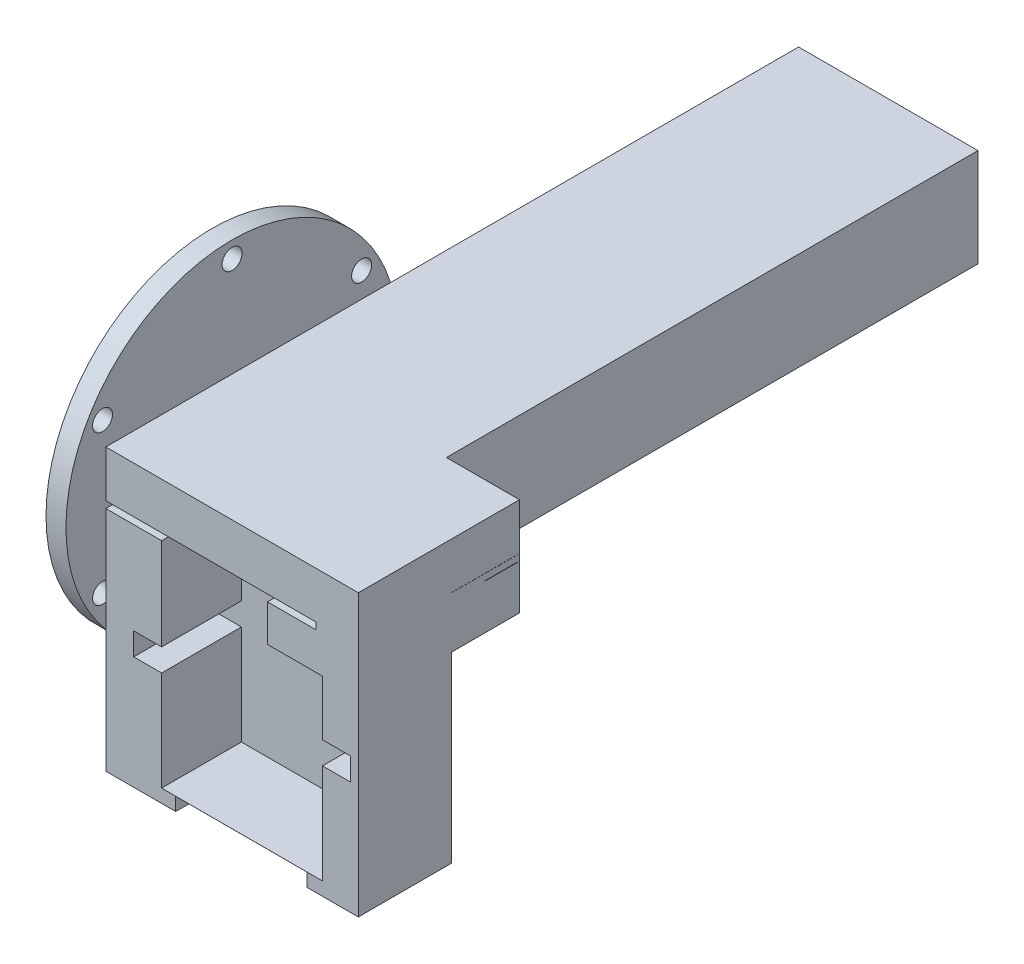
SolidWorks part; units mm, degrees
ref_plane "前视基准面" through (0, 0, 0) normal (0, 0, 1) x (1, 0, 0)
ref_plane "上视基准面" through (0, 0, 0) normal (0, 1, 0) x (1, 0, 0)
ref_plane "右视基准面" through (0, 0, 0) normal (1, 0, 0) x (0, 0, -1)
sketch "草图2" plane through (0, 0, 6) normal (0, 0, 1) x (1, 0, 0)
  line L0 (29.8673, 15.5624) -> (29.0149, 15.5624)
  line L1 (29.0149, 15.5624) -> (29.0149, 12.2624)
  line L2 (29.0149, 12.2624) -> (24.8149, 12.2624)
  line L3 (24.8149, 12.2624) -> (24.8149, 8.8624)
  line L4 (24.8149, 8.8624) -> (29.0149, 8.8624)
  line L5 (29.0149, 8.8624) -> (29.0149, -6.1376)
  line L6 (29.0149, -6.1376) -> (53.2196, -6.1376)
  line L8 (58.6173, -8.1376) -> (23.6173, -8.1376)
  line L9 (23.6173, -8.1376) -> (23.6173, 15.5624)
  line L10 (23.6173, 15.5624) -> (29.0149, 15.5624)
  line L11 (58.6173, 15.5624) -> (53.2196, 15.5624)
  line L12 (58.6173, -8.1376) -> (58.6173, 15.5624)
  line L13 (53.2196, 8.8624) -> (53.2196, -6.1376)
  line L14 (57.4196, 8.8624) -> (53.2196, 8.8624)
  line L15 (57.4196, 12.2624) -> (57.4196, 8.8624)
  line L16 (53.2196, 12.2624) -> (57.4196, 12.2624)
  line L17 (53.2196, 15.5624) -> (53.2196, 12.2624)
extrude "凸台-拉伸1" add sketch "草图2" against normal blind 14 contours L11 L17 L16 L15 L14 L13 L6 L5 L4 L3 L2 L1 L10 L9 L8 L12
sketch "草图3" plane through (0, 0, -8) normal (0, 0, -1) x (-1, 0, 0)
  line L0 (-58.6173, -8.1376) -> (-23.6173, -8.1376) construction
  line L1 (-58.6173, 15.5624) -> (-23.6281, 15.5624)
  line L2 (-58.6173, 15.5624) -> (-58.6173, -8.1376)
  line L3 (-58.6173, -8.1376) -> (-23.6281, -8.1376)
  line L4 (-23.6281, 15.5624) -> (-23.6281, -8.1376)
extrude "凸台-拉伸2" add sketch "草图3" against normal blind 1.99
sketch "草图4" plane through (0, -8.1376, 0) normal (0, -1, 0) x (1, 0, 0)
  line L0 (58.6173, 6) -> (23.6173, 6) construction
  line L1 (31.1325, 6) -> (50.872, 6)
  line L2 (31.1325, 6) -> (31.1325, -8)
  line L3 (31.1325, -8) -> (50.872, -8)
  line L4 (50.872, 6) -> (50.872, -8)
  line L5 (58.6173, -8) -> (23.6173, -8) construction
extrude "切除-拉伸1" cut sketch "草图4" against normal blind 1.99
sketch "草图5" plane through (0, 27.1124, 0) normal (0, 1, 0) x (1, 0, 0)
  circle A0 centre (35.6173, 0) radius 17.25
sketch "草图6" plane through (0, 26.1124, 0) normal (0, -1, 0) x (1, 0, 0)
  line L0 (35.6173, -17.25) -> (35.6173, -8.75)
  line L1 (35.6173, 17.25) -> (35.6173, 8.75)
  line L2 (35.6173, 8.75) -> (20.7512, 8.75)
  line L3 (35.6173, 8.75) -> (50.4833, 8.75)
  circle A0 centre (35.6173, 0) radius 17.25
sketch "草图7" plane through (0, 15.5624, 0) normal (0, 1, 0) x (1, 0, 0)
  line L0 (23.6173, -6) -> (23.6173, 8)
  line L1 (23.6173, 8) -> (23.6173, -6) construction
  line L2 (58.6173, 8) -> (23.6173, 8) construction
  line L3 (23.6173, 8) -> (58.6173, 8)
  line L4 (58.6173, 8) -> (58.6173, -6)
  line L5 (58.6173, -6) -> (53.2196, -6) construction
  line L6 (58.6173, 8) -> (58.6173, -6) construction
  line L7 (58.6173, -6) -> (53.2196, -6)
  line L8 (53.2196, -6) -> (53.2196, 6.01)
  line L9 (53.2196, 6.01) -> (29.0149, 6.01)
  line L10 (29.0149, 6.01) -> (29.0149, -6)
  line L11 (29.0149, -6) -> (23.6173, -6)
extrude "凸台-拉伸3" add sketch "草图7" along normal blind 4.99 contours L11 L0 L3 L4 L7 L8 L9 L10
sketch "草图8" plane through (0, 20.5524, 0) normal (0, 1, 0) x (1, 0, 0)
  line L0 (23.6173, -6) -> (29.0149, -6)
  line L1 (23.6173, 8) -> (23.6173, -6) construction
  line L2 (23.6173, -6) -> (29.0149, -6) construction
  line L3 (29.0149, -6) -> (29.0149, 6.01)
  line L4 (29.0149, 6.01) -> (44.9535, 6.01)
  line L5 (29.0149, 6.01) -> (53.2196, 6.01) construction
  line L6 (44.9535, 6.01) -> (44.9535, -6)
  line L7 (44.9535, -6) -> (58.6173, -6)
  line L8 (58.6173, -6) -> (58.6173, 8) construction
  line L9 (58.6173, -6) -> (58.6173, 8)
  line L10 (58.6173, 8) -> (23.6173, 8)
  line L11 (58.6173, 8) -> (23.6173, 8) construction
  line L12 (23.6173, 8) -> (23.6173, -6)
extrude "凸台-拉伸4" add sketch "草图8" along normal blind 5.55 contours L12 L0 L3 L4 L6 L7 L9 L10
sketch "草图11" plane through (0, 26.1024, 0) normal (0, 1, 0) x (1, 0, 0)
  line L0 (51.3501, 8) -> (58.6173, 8)
  line L1 (58.6173, 8) -> (23.6173, 8) construction
  line L2 (58.6173, 8) -> (58.6173, -6)
  line L3 (44.9535, -6) -> (58.6173, -6) construction
  line L4 (58.6173, -6) -> (58.6173, 8) construction
  line L5 (58.6173, -6) -> (52.2161, -6)
  arc A0 (52.2161, -6) -> (51.3501, 8) centre (35.6173, 0) ccw
extrude "凸台-拉伸5" add sketch "草图11" along normal blind 1.02
sketch "草图13" plane through (0, 27.1224, 0) normal (0, 1, 0) x (1, 0, 0)
  line L0 (23.6173, -6) -> (29.0149, -6) construction
  line L1 (58.6173, 8) -> (23.6173, 8)
  line L2 (58.6173, 8) -> (58.6173, -6)
  line L3 (58.6173, -6) -> (23.6173, -6)
  line L4 (23.6173, 8) -> (23.6173, -6)
  line L5 (23.6173, 8) -> (23.6173, -6) construction
extrude "凸台-拉伸6" add sketch "草图13" along normal blind 4
sketch "草图14" plane through (23.6173, 0, 0) normal (-1, 0, 0) x (0, 0, 1)
  line L0 (-8, 27.1224) -> (-8, 26.1024)
  line L1 (-8, 26.6124) -> (-13, 26.6124)
  line L2 (-8, 26.1024) -> (-8.7807, 26.1024)
  line L3 (-8, 27.1224) -> (-8.7807, 27.1224)
  line L4 (-13, 30.8624) -> (-8, 30.8624)
  line L5 (-8, 31.1224) -> (-8, 27.1224) construction
  line L6 (-13, 22.3624) -> (-8, 22.3624)
  line L7 (-8, -8.1376) -> (-8, 26.1024) construction
  line L8 (-8, 30.8624) -> (-8, 22.3624)
  line L9 (-8, 30.8624) -> (-8, 31.1224)
  line L10 (-8, 31.1224) -> (-13, 31.1224)
  line L11 (-13, 31.1224) -> (-13, 30.8624)
  line L12 (-13, 22.3624) -> (-13, 20.3624)
  line L13 (-13, 20.3624) -> (-8, 20.3624)
  line L14 (-8, 20.3624) -> (-8, 22.3624)
  circle A1 centre (-13, 26.6124) radius 4.25
  line M3 (-8, 26.1024) -> (-8, -8.1376)
extrude "凸台-拉伸8" add sketch "草图14" against normal blind 21 contours L12 L13 L6 M3 | A1 L6 L2 M3 | A1 L3 L8 L4
sketch "草图15" plane through (44.6173, 0, 0) normal (1, 0, 0) x (0, 0, -1)
  line L2 (13, 20.3624) -> (8, 20.3624)
  line L3 (13, 20.3624) -> (13, 26.1024)
  line L4 (13, 26.1024) -> (8, 26.1024)
  line L5 (8, 20.3624) -> (8, 26.1024)
  line L6 (13, 31.1224) -> (8, 31.1224)
  line L7 (13, 31.1224) -> (13, 27.1224)
  line L8 (13, 27.1224) -> (8, 27.1224)
  line L9 (8, 31.1224) -> (8, 27.1224)
extrude "凸台-拉伸9" add sketch "草图15" along normal blind 14
sketch "草图16" plane through (0, 26.1024, 0) normal (0, 1, 0) x (1, 0, 0)
  line L0 (47.4815, 13) -> (58.6173, 13)
  line L1 (58.6173, 13) -> (44.6173, 13) construction
  line L2 (58.6173, 13) -> (58.6173, 8)
  line L3 (58.6173, 13) -> (58.6173, 8) construction
  line L4 (58.6173, 8) -> (51.294, 8)
  arc A0 (51.294, 8) -> (47.4815, 13) centre (35.6173, 0) ccw
extrude "凸台-拉伸10" add sketch "草图16" along normal blind 1
sketch "草图17" plane through (0, 31.1224, 0) normal (0, 1, 0) x (1, 0, 0)
  line L0 (23.6173, -6) -> (58.6173, -6) construction
  line L1 (23.6173, 13) -> (58.6173, 13)
  line L2 (23.6173, 13) -> (23.6173, -6)
  line L3 (23.6173, -6) -> (58.6173, -6)
  line L4 (58.6173, 13) -> (58.6173, -6)
extrude "凸台-拉伸11" add sketch "草图17" along normal blind 3
sketch "草图18" plane through (0, 20.3624, 0) normal (0, -1, 0) x (1, 0, 0)
  line L1 (23.6173, -8) -> (58.6173, -8)
  line L2 (23.6173, -8) -> (23.6173, -13)
  line L3 (23.6173, -13) -> (58.6173, -13)
  line L4 (58.6173, -8) -> (58.6173, -13)
extrude "凸台-拉伸12" add sketch "草图18" along normal blind 1
sketch "草图19" plane through (23.6173, 0, 0) normal (-1, 0, 0) x (0, 0, 1)
  line L0 (-8, 19.3624) -> (-17.25, 19.3624)
  line L1 (6, -8.1376) -> (-8, -8.1376)
  line L2 (6, -8.1376) -> (6, 19.3624)
  line L3 (6, 19.3624) -> (-8, 19.3624)
  line L4 (-8, -8.1376) -> (-8, 19.3624)
  line L13 (-17.25, 19.3624) -> (-17.25, 34.1224)
  line L14 (-17.25, 34.1224) -> (6, 34.1224)
  line L15 (6, 34.1224) -> (6, 27.1224)
  line L16 (6, 34.1224) -> (6, 27.1224) construction
  line L17 (6, 27.1224) -> (-8.7807, 27.1224)
  line L18 (-8.7807, 26.1024) -> (6, 26.1024)
  line L19 (6, 26.1024) -> (6, 19.3624)
  line L20 (-17.25, 19.3624) -> (6, 19.3624)
  line L21 (-13, 22.3624) -> (-17.25, 22.3624)
  line L22 (-13, 30.8624) -> (-17.25, 30.8624)
  line L23 (-17.25, 19.3624) -> (-18.25, 19.3624)
  line L24 (-18.25, 19.3624) -> (-18.25, 34.1224)
  line L25 (-18.25, 34.1224) -> (-17.25, 34.1224)
  line L26 (-18.25, 34.1224) -> (-17.25, 34.1224)
  line L27 (-18.25, 19.3624) -> (-17.25, 19.3624)
  circle A0 centre (-13, 26.6124) radius 4.25
  line M14 (6, -8.1376) -> (6, 26.1024)
  line M15 (6, 26.1024) -> (-8.7807, 26.1024)
  arc M16 (-8.7807, 26.1024) -> (-13, 22.3624) centre (-13, 26.6124) cw
  line M17 (-13, 22.3624) -> (-13, 19.3624)
  line M18 (-13, 19.3624) -> (-8, 19.3624)
  line M19 (-8, 19.3624) -> (-8, -8.1376)
  line M20 (-8, -8.1376) -> (6, -8.1376)
extrude "凸台-拉伸16" add sketch "草图19" along normal blind 3 contours L3 M14 M15 M16 M17 M18 | A0 L17 L15 L14 L13 L22 | L21 L13 L0 M17 | L3 M14 M19 M20 | L25 L24 L23 L13 | A0 L13 L21 | A0 L22 L13
sketch "草图20" plane through (23.6173, 0, 0) normal (1, 0, 0) x (0, 0, -1)
  line L0 (13, 19.3624) -> (18.25, 19.3624)
  line L1 (18.25, 19.3624) -> (18.25, 22.3624)
  line L2 (18.25, 19.3624) -> (18.25, 34.1224) construction
  line L3 (18.25, 22.3624) -> (13, 22.3624)
  line L4 (13, 30.8624) -> (18.25, 30.8624)
  line L5 (13, 34.1224) -> (13, 30.8624) construction
  line L6 (18.25, 30.8624) -> (18.25, 34.1224)
  line L7 (18.25, 34.1224) -> (13, 34.1224) construction
  line L8 (18.25, 34.1224) -> (13, 34.1224)
  line L9 (13, 34.1224) -> (13, 30.8624)
  arc A0 (13, 22.3624) -> (13, 30.8624) centre (13, 26.6124) ccw construction
  line M1 (13, 22.3624) -> (13, 19.3624)
  line M2 (13, 19.3624) -> (18.25, 19.3624)
  line M3 (18.25, 19.3624) -> (18.25, 34.1224)
  line M4 (18.25, 34.1224) -> (13, 34.1224)
  line M5 (13, 34.1224) -> (13, 30.8624)
extrude "凸台-拉伸18" add sketch "草图20" along normal blind 35 contours L4 M5 M3 M4 | L3 M3 M1 M2
sketch "草图21" plane through (0, 0, -13) normal (0, 0, -1) x (-1, 0, 0)
  line L0 (-58.6173, 22.3624) -> (-58.6173, 27.1024) construction
  line L1 (-58.6173, 30.8624) -> (-44.6173, 30.8624)
  line L2 (-58.6173, 30.8624) -> (-58.6173, 27.1224)
  line L3 (-58.6173, 27.1224) -> (-44.6173, 27.1224)
  line L4 (-44.6173, 30.8624) -> (-44.6173, 27.1224)
  line L5 (-44.6173, 22.3624) -> (-58.6173, 22.3624)
  line L6 (-44.6173, 22.3624) -> (-44.6173, 26.1124)
  line L7 (-44.6173, 26.1124) -> (-58.6173, 26.1124)
  line L8 (-58.6173, 22.3624) -> (-58.6173, 26.1124)
extrude "凸台-拉伸19" add sketch "草图21" along normal blind 5
sketch "草图22" plane through (58.6173, 0, 0) normal (1, 0, 0) x (0, 0, -1)
  line L0 (18.25, 22.3624) -> (18.25, 30.8624) construction
  line L1 (13, 27.1024) -> (18.25, 27.1024)
  line L2 (13, 27.1024) -> (13, 26.1558)
  line L3 (13, 26.1558) -> (18.25, 26.1558)
  line L4 (18.25, 27.1024) -> (18.25, 26.1558)
  line L6 (18, 30.8624) -> (18.25, 30.8624)
  line L7 (18, 30.8624) -> (18, 22.3624)
  line L8 (18, 22.3624) -> (18.25, 22.3624)
  line L9 (18.25, 30.8624) -> (18.25, 22.3624)
  line M2 (13, 26.1124) -> (13, 27.1024)
extrude "凸台-拉伸20" add sketch "草图22" against normal blind 11 contours L7 L1 L3 M2
ref_plane "基准面5" through (47.6173, 30.8624, -18.25) normal (0, -1, 0) x (-1, 0, 0)
sketch "草图26" plane through (47.6173, 0, 0) normal (-1, 0, 0) x (0, 0, 1)
  line L0 (-20.5875, 30.8624) -> (-15.9125, 30.8624) construction
  line L1 (-18.25, 30.8624) -> (-18, 30.8624)
  line L2 (-18.25, 30.8624) -> (-18.25, 22.3624)
  line L3 (-18.25, 22.3624) -> (-18, 22.3624)
  line L4 (-18, 30.8624) -> (-18, 22.3624)
  line L5 (-18.25, 19.3624) -> (-18.25, 34.1224) construction
  line L6 (-18, 26.1124) -> (-18, 22.3624) construction
extrude "凸台-拉伸21" add sketch "草图26" along normal blind 3 contours L2 L1 L4 L3
sketch "草图27" plane through (0, 0, -18.25) normal (0, 0, -1) x (-1, 0, 0)
  line L0 (-49.9548, 30.8624) -> (-45.2798, 30.8624) construction
  line L1 (-44.6173, 30.8624) -> (-23.6173, 30.8624)
  line L2 (-44.6173, 30.8624) -> (-44.6173, 22.3624)
  line L3 (-44.6173, 22.3624) -> (-23.6173, 22.3624)
  line L4 (-23.6173, 30.8624) -> (-23.6173, 22.3624)
  line L5 (-44.6173, 30.8624) -> (-44.6173, 22.3624) construction
  line L6 (-44.6173, 30.8624) -> (-47.6173, 30.8624)
  line L7 (-20.6173, 19.3624) -> (-58.6173, 19.3624) construction
  line L8 (-20.6173, 34.1224) -> (-47.6173, 34.1224)
  line L9 (-20.6173, 34.1224) -> (-20.6173, 19.3624)
  line L10 (-20.6173, 19.3624) -> (-47.6173, 19.3624)
  line L11 (-47.6173, 34.1224) -> (-47.6173, 19.3624)
extrude "凸台-拉伸22" add sketch "草图27" along normal blind 80
sketch "草图28" plane through (20.6173, 0, 0) normal (-1, 0, 0) x (0, 0, 1)
  line L0 (-13, 26.6124) -> (-13, 4.1024)
  circle A0 centre (-13, 26.6124) radius 25
  circle A1 centre (-13, 26.6124) radius 6
  circle A2 centre (-13, 4.1024) radius 1.5
  circle A3 centre (-32.4942, 15.3574) radius 1.5
  circle A4 centre (-32.4942, 37.8674) radius 1.5
  circle A5 centre (-13, 49.1224) radius 1.5
  circle A6 centre (6.4942, 37.8674) radius 1.5
  circle A7 centre (6.4942, 15.3574) radius 1.5
  point P19 (-13, 26.6124)
  dimension "D1" = 6
extrude "凸台-拉伸23" add sketch "草图28" along normal blind 3
